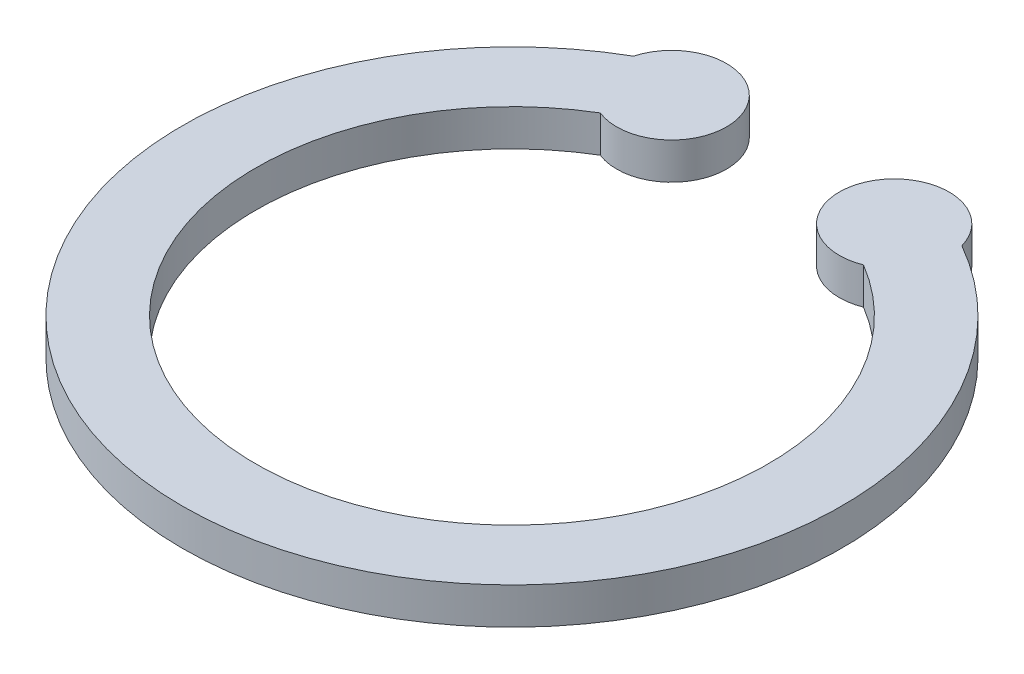
SolidWorks part; units mm, degrees
ref_plane "Front Plane" through (0, 0, 0) normal (0, 0, 1) x (1, 0, 0)
ref_plane "Top Plane" through (0, 0, 0) normal (0, 1, 0) x (1, 0, 0)
ref_plane "Right Plane" through (0, 0, 0) normal (1, 0, 0) x (0, 0, -1)
sketch "Sketch1" plane through (0, 0, 0) normal (0, 1, 0) x (1, 0, 0)
  arc A0 (-1.7971, 3.0034) -> (1.7971, 3.0034) centre (0, 0) ccw
  arc A1 (-2.2419, 3.9018) -> (2.2419, 3.9018) centre (0, 0) ccw
  arc A2 (-1.7971, 3.0034) -> (-2.2419, 3.9018) centre (-1.5196, 3.7001) ccw
  arc A3 (2.2419, 3.9018) -> (1.7971, 3.0034) centre (1.5196, 3.7001) ccw
  dimension "D1" = 7
  dimension "D2" = 9
  dimension "D3" = 1.5
  dimension "D4" = 1.5
extrude "Boss-Extrude1" add sketch "Sketch1" along normal blind 0.5
